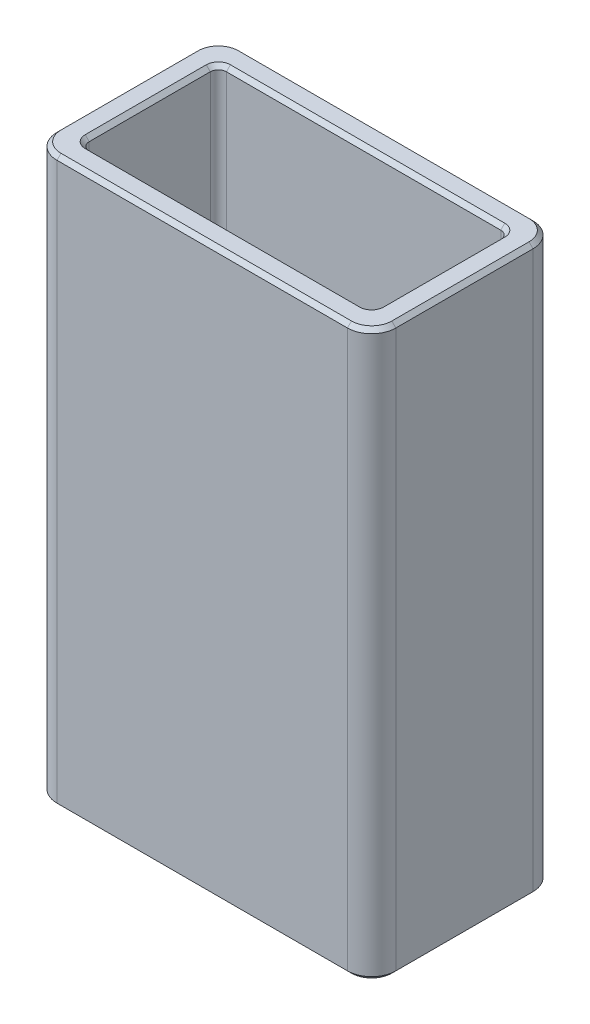
SolidWorks part; units mm, degrees
ref_plane "Alzado" through (0, 0, 0) normal (0, 0, 1) x (1, 0, 0)
ref_plane "Planta" through (0, 0, 0) normal (0, 1, 0) x (1, 0, 0)
ref_plane "Vista lateral" through (0, 0, 0) normal (1, 0, 0) x (0, 0, -1)
sketch "Croquis1" plane through (0, 0, 0) normal (0, 1, 0) x (1, 0, 0)
  line L0 (-21, 11.5) -> (21, 11.5)
  line L1 (-18, -8.5) -> (18, -8.5)
  line L2 (-18, -8.5) -> (-18, 8.5)
  line L3 (-18, 8.5) -> (18, 8.5)
  line L4 (18, -8.5) -> (18, 8.5)
  line L5 (-18, -8.5) -> (18, 8.5) construction
  line L6 (-18, 8.5) -> (18, -8.5) construction
  line L7 (21, -11.5) -> (21, 11.5)
  line L8 (-21, -11.5) -> (21, -11.5)
  line L9 (-21, -11.5) -> (-21, 11.5)
  point P0 (0, 0)
  dimension "D1" = 36
  dimension "D2" = 17
  dimension "D3" = 3
extrude "Saliente-Extruir1" add sketch "Croquis1" along normal blind 70
fillet "Redondeo1" radius 3 4 edges at (-21, 35, -11.5) (21, 35, -11.5) (21, 35, 11.5) (-21, 35, 11.5)
fillet "Redondeo2" radius 1 4 edges at (18, 35, 8.5) (18, 35, -8.5) (-18, 35, -8.5) (-18, 35, 8.5)
chamfer "Chaflán1" distance 0.5 angle 45 32 edges at (-17.7071, 0, -8.2071) (0, 0, -8.5) (17.7071, 0, -8.2071) (18, 0, 0) (17.7071, 0, 8.2071) (0, 0, 8.5) (-17.7071, 0, 8.2071) (-18, 0, 0) (-20.1213, 0, 10.6213) (0, 0, 11.5) (20.1213, 0, 10.6213) (21, 0, 0) (20.1213, 0, -10.6213) (0, 0, -11.5) (-20.1213, 0, -10.6213) (-21, 0, 0) (17.7071, 70, -8.2071) (0, 70, -8.5) (-17.7071, 70, -8.2071) (-18, 70, 0) (-17.7071, 70, 8.2071) (0, 70, 8.5) (17.7071, 70, 8.2071) (18, 70, 0) (20.1213, 70, -10.6213) (21, 70, 0) (20.1213, 70, 10.6213) (0, 70, 11.5) (-20.1213, 70, 10.6213) (-21, 70, 0) (-20.1213, 70, -10.6213) (0, 70, -11.5)
